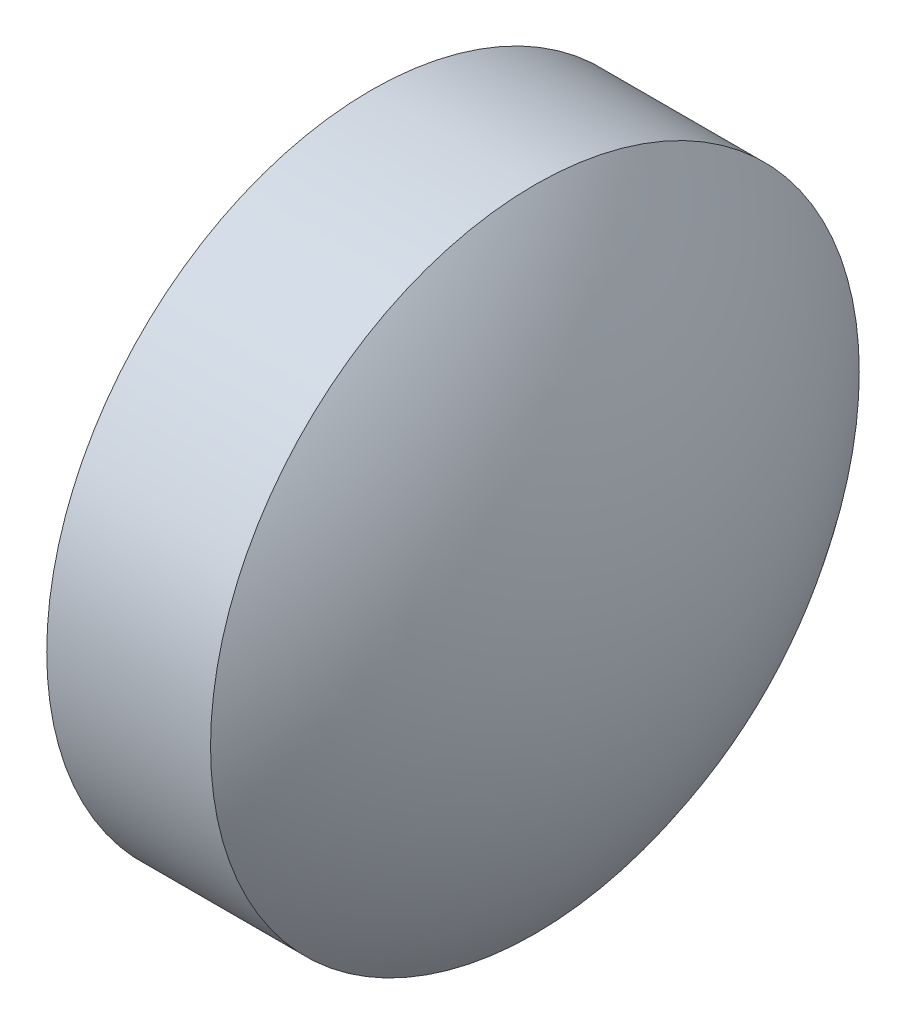
SolidWorks part; units mm, degrees
ref_plane "前视基准面" through (0, 0, 0) normal (0, 0, 1) x (1, 0, 0)
ref_plane "上视基准面" through (0, 0, 0) normal (0, 1, 0) x (1, 0, 0)
ref_plane "右视基准面" through (0, 0, 0) normal (1, 0, 0) x (0, 0, -1)
sketch "草图1" plane through (0, 0, 0) normal (0, 0, 1) x (1, 0, 0)
  line L0 (506.8799, -76.1335) -> (505.1799, -76.1335)
  line L7 (504.75, -76.1335) -> (507.4475, -76.1335) construction
  line L8 (505.1799, -76.1335) -> (505.1799, -74.1335)
  line L9 (505.1799, -74.1335) -> (506.1899, -74.1335)
  arc A1 (506.8799, -76.1335) -> (506.1899, -74.1335) centre (503.6363, -76.1335) ccw
revolve "旋转2" add sketch "草图1" angle 360 about L7
